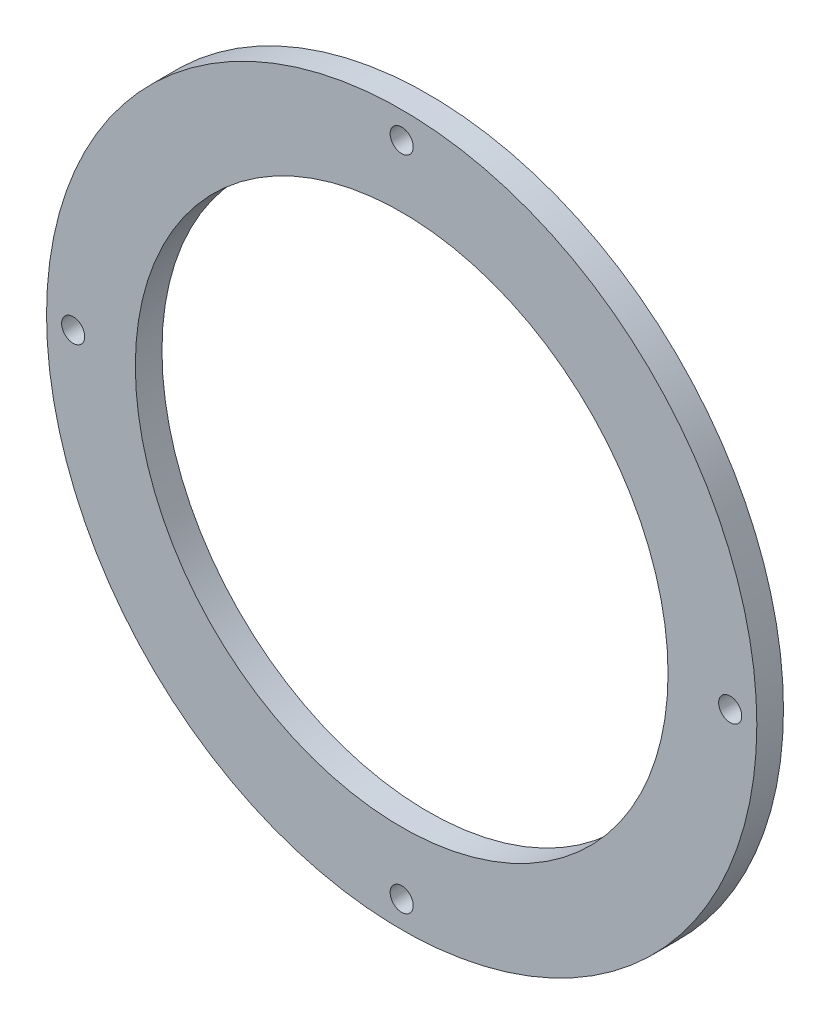
SolidWorks part; units mm, degrees
material "Alliage 1060"
ref_plane "Plan de face" through (0, 0, 0) normal (0, 0, 1) x (1, 0, 0)
ref_plane "Plan de dessus" through (0, 0, 0) normal (0, 1, 0) x (1, 0, 0)
ref_plane "Plan de droite" through (0, 0, 0) normal (1, 0, 0) x (0, 0, -1)
sketch "Esquisse1" plane through (0, 0, 0) normal (0, 0, 1) x (1, 0, 0)
  circle A0 centre (0, 0) radius 40
  dimension "D1" = 80
extrude "Boss.-Extru.1" add sketch "Esquisse1" along normal blind 3
hole_wizard "Dégagement M21" positions "Esquisse2" profile "Esquisse3" hole size "M2" standard "ISO" end condition through all
sketch "Esquisse2" plane through (0, 0, 0) normal (0, 0, -1) x (-1, 0, 0)
  point P0 (0, 37)
  dimension "D1" = 37
sketch "Esquisse3" plane through (0, 37, 0) normal (1, 0, 0) x (0, 1, 0)
  line L0 (0, 0) -> (0, 3)
  line L1 (0, 3) -> (1.3, 3)
  line L2 (1.3, 3) -> (1.3, 0)
  line L5 (1.3, 0) -> (0, 0)
  line L11 (0, -6.35) -> (0, 107.95) construction
  dimension "Diamètre du perçage jusqu'au prochain" = 2.6
  dimension "Profondeur du perçage jusqu'au prochain" = 3
pattern_circular "Répétition circulaire1" count 4 over 360 about axis through (0, 0, 0) along (0, 0, 1) of "Dégagement M21"
sketch "Esquisse4" plane through (0, 0, 0) normal (0, 0, -1) x (-1, 0, 0)
  circle A0 centre (0, 0) radius 30
  dimension "D1" = 60
extrude "Enlèv. mat.-Extru.1" cut sketch "Esquisse4" against normal blind 10
